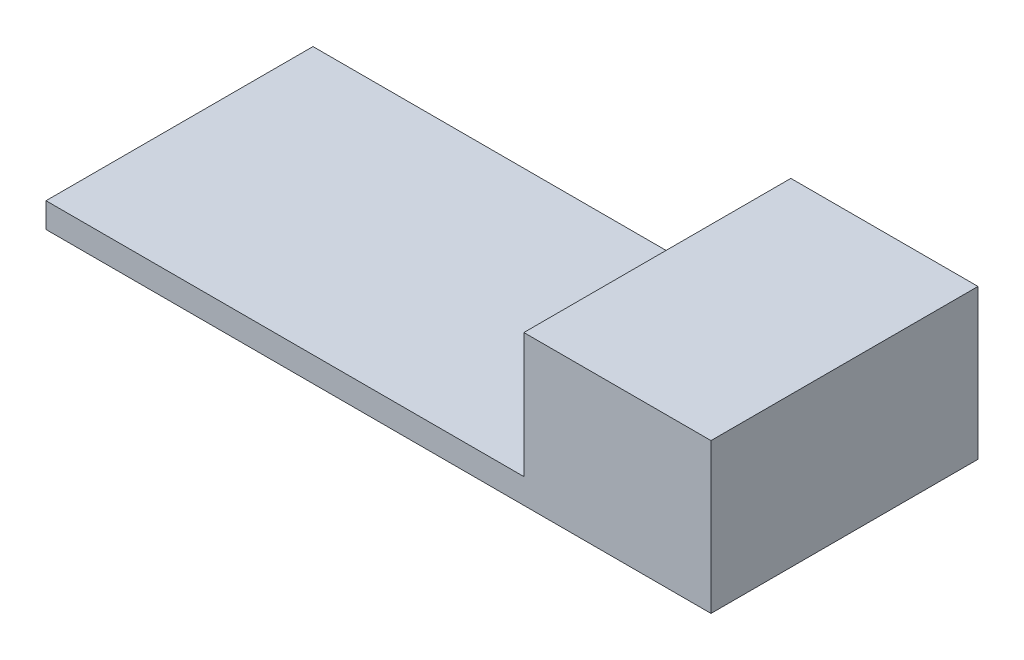
SolidWorks part; units mm, degrees
ref_plane "Front Plane" through (0, 0, 0) normal (0, 0, 1) x (1, 0, 0)
ref_plane "Top Plane" through (0, 0, 0) normal (0, 1, 0) x (1, 0, 0)
ref_plane "Right Plane" through (0, 0, 0) normal (1, 0, 0) x (0, 0, -1)
sketch "Sketch1" plane through (0, 0, 0) normal (0, 1, 0) x (1, 0, 0)
  line L1 (-26.65, -10.7) -> (26.65, -10.7)
  line L2 (-26.65, -10.7) -> (-26.65, 10.7)
  line L3 (-26.65, 10.7) -> (26.65, 10.7)
  line L4 (26.65, -10.7) -> (26.65, 10.7)
  line L5 (-26.65, -10.7) -> (26.65, 10.7) construction
  line L6 (-26.65, 10.7) -> (26.65, -10.7) construction
  point P0 (0, 0)
  dimension "D1" = 21.4
  dimension "D2" = 53.3
extrude "Boss-Extrude1" add sketch "Sketch1" along normal blind 2
sketch "Sketch2" plane through (0, 2, 0) normal (0, 1, 0) x (1, 0, 0)
  line L0 (26.65, 10.7) -> (-26.65, 10.7) construction
  line L1 (26.65, -10.7) -> (11.65, -10.7)
  line L2 (26.65, -10.7) -> (26.65, 10.7)
  line L3 (26.65, 10.7) -> (11.65, 10.7)
  line L4 (11.65, -10.7) -> (11.65, 10.7)
  dimension "D1" = 15
extrude "Boss-Extrude2" add sketch "Sketch2" along normal blind 10
